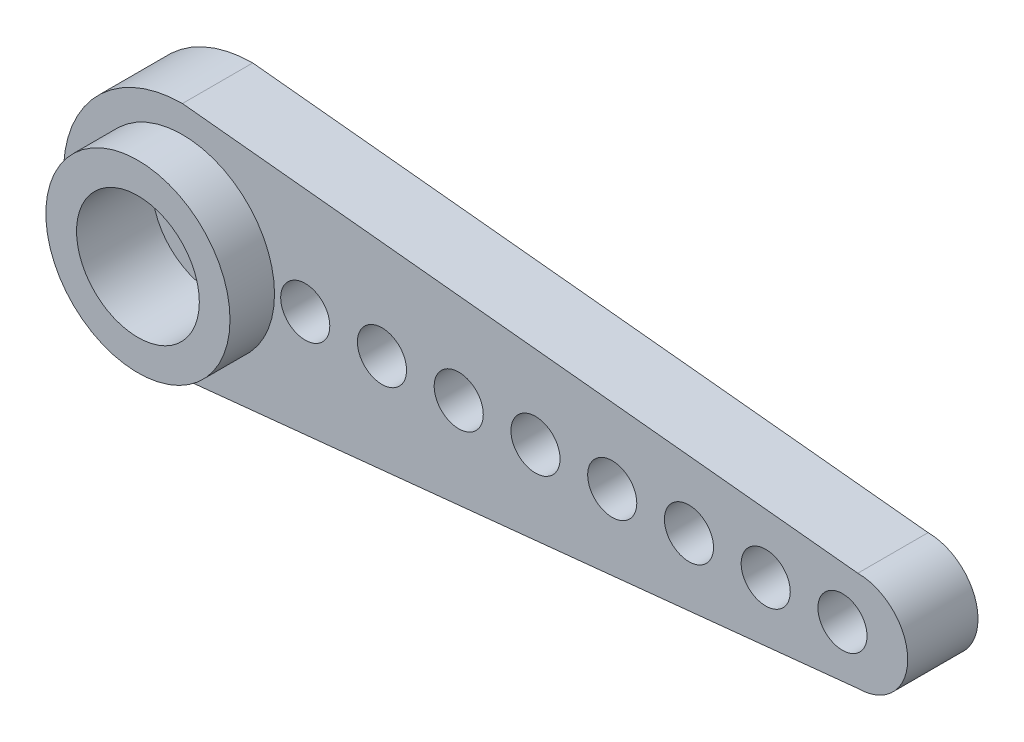
SolidWorks part; units mm, degrees
ref_plane "Front Plane" through (0, 0, 0) normal (0, 0, 1) x (1, 0, 0)
ref_plane "Top Plane" through (0, 0, 0) normal (0, 1, 0) x (1, 0, 0)
ref_plane "Right Plane" through (0, 0, 0) normal (1, 0, 0) x (0, 0, -1)
sketch "草圖1" plane through (0, 0, 0) normal (0, 0, 1) x (1, 0, 0)
  line L0 (-7.75, 0) -> (47.25, 0) construction
  line L1 (0, 7.75) -> (44, 3.25)
  line L2 (0, -7.75) -> (44, -3.25)
  arc A0 (1.5688, 7.5896) -> (1.5688, -7.5896) centre (0, 0) ccw
  arc A1 (44, -3.25) -> (44, 3.25) centre (44, 0) ccw
  dimension "D1" = 15.5
  dimension "D3" = 6.5
  dimension "D2" = 55
extrude "填料-伸長1" add sketch "草圖1" along normal blind 4.58 contours A0 L0 A1 L1 | L0 A0 L2 A1
sketch "草圖2" plane through (0, 0, 4.58) normal (0, 0, 1) x (1, 0, 0)
  circle A0 centre (0, 0) radius 6
  dimension "D1" = 12
extrude "填料-伸長2" add sketch "草圖2" along normal blind 2.9
sketch "草圖3" plane through (0, 0, 7.48) normal (0, 0, 1) x (1, 0, 0)
  circle A0 centre (0, 0) radius 4
  dimension "D1" = 8
extrude "除料-伸長1" cut sketch "草圖3" against normal blind 4.935
sketch "草圖6" plane through (0, 0, 0) normal (0, 0, -1) x (-1, 0, 0)
  circle A0 centre (0, 0) radius 4.65
  dimension "D1" = 9.3
extrude "填料-伸長3" add sketch "草圖6" along normal blind 0.4
sketch "草圖7" plane through (0, 0, -0.4) normal (0, 0, -1) x (-1, 0, 0)
  circle A0 centre (0, 0) radius 3.8
  circle A1 centre (0, 0) radius 4.65 construction
  dimension "D1" = 0.85
extrude "除料-伸長4" cut sketch "草圖7" against normal blind 0.9
sketch "草圖4" plane through (0, 0, 2.545) normal (0, 0, 1) x (1, 0, 0)
  circle A0 centre (0, 0) radius 1.575
  dimension "D1" = 3.15
extrude "除料-伸長2" cut sketch "草圖4" against normal through all
sketch "草圖5" plane through (0, 0, 0) normal (0, 0, -1) x (-1, 0, 0)
  line L0 (-8, 0) -> (0, 0) construction
  circle A0 centre (-8, 0) radius 1.6
  dimension "D2" = 3.2
  dimension "D1" = 8
extrude "除料-伸長3" cut sketch "草圖5" against normal through all
pattern_linear "直線複製排列1" count 8 spacing 5 along (1, 0, 0) of "除料-伸長3"
